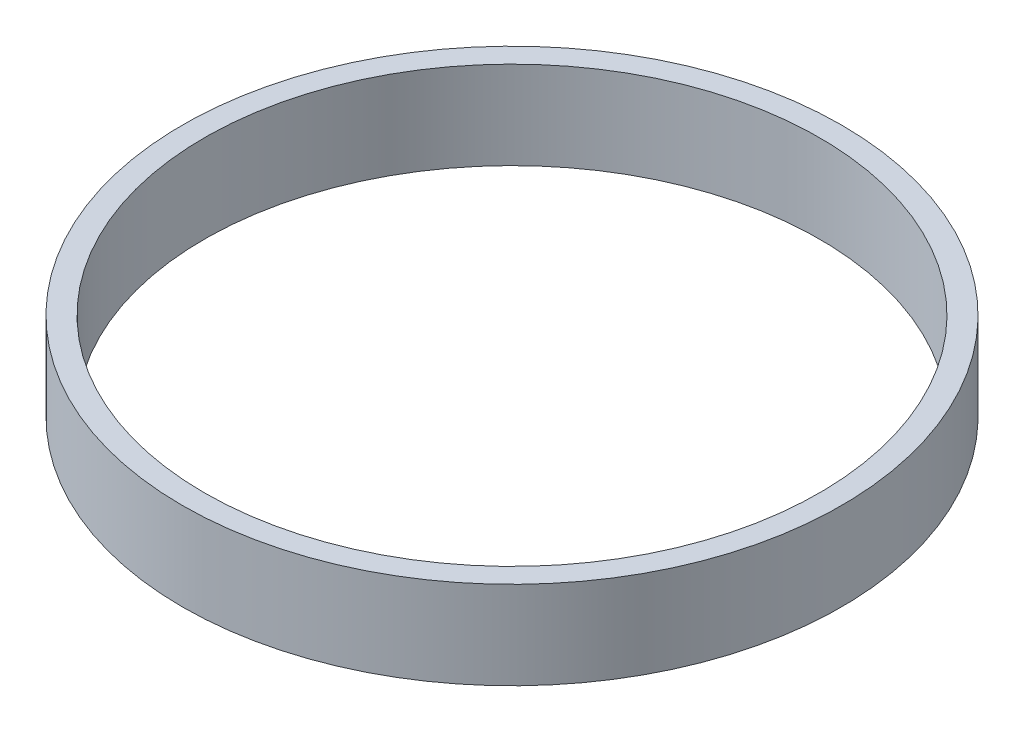
SolidWorks part; units mm, degrees
material "PP Copolymer"
ref_plane "Front Plane" through (0, 0, 0) normal (0, 0, 1) x (1, 0, 0)
ref_plane "Top Plane" through (0, 0, 0) normal (0, 1, 0) x (1, 0, 0)
ref_plane "Right Plane" through (0, 0, 0) normal (1, 0, 0) x (0, 0, -1)
sketch "Sketch1" plane through (0, 0, 0) normal (0, 1, 0) x (1, 0, 0)
  circle A0 centre (0, 0) radius 37.5
  circle A1 centre (0, 0) radius 35
  dimension "D1" = 75
  dimension "D2" = 2.5
extrude "Boss-Extrude1" add sketch "Sketch1" along normal blind 10
